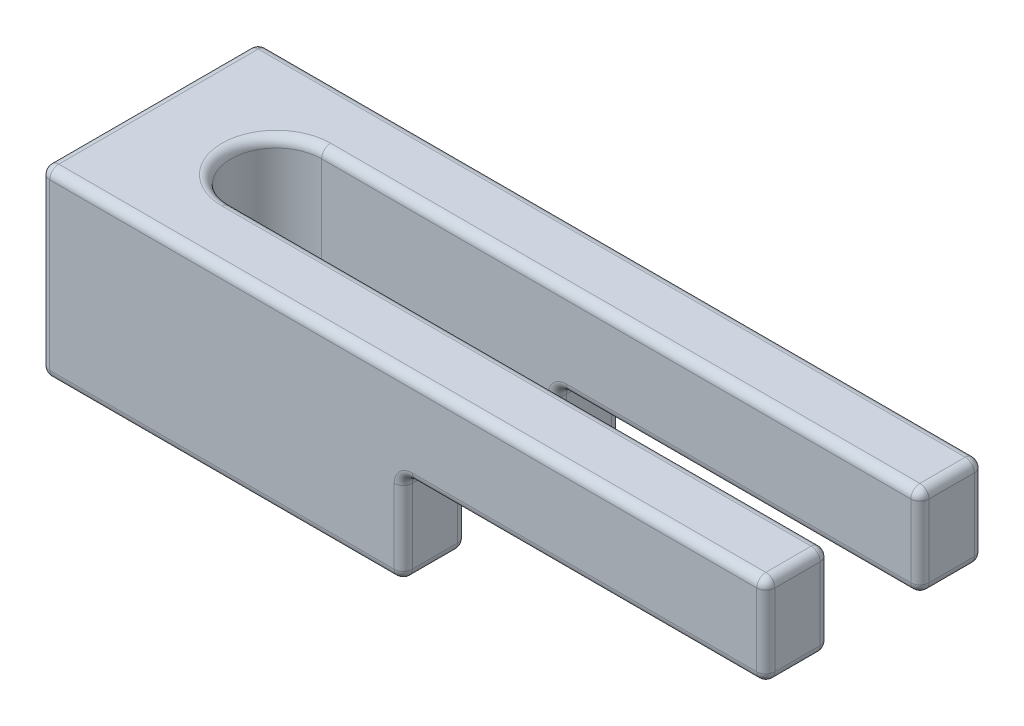
SolidWorks part; units mm, degrees
ref_plane "Plan de face" through (0, 0, 0) normal (0, 0, 1) x (1, 0, 0)
ref_plane "Plan de dessus" through (0, 0, 0) normal (0, 1, 0) x (1, 0, 0)
ref_plane "Plan de droite" through (0, 0, 0) normal (1, 0, 0) x (0, 0, -1)
sketch "Esquisse1" plane through (0, 0, 0) normal (0, 1, 0) x (1, 0, 0)
  line L0 (-88, 0) -> (88, 0) construction
  line L1 (-95, -6) -> (95, -6)
  line L2 (-95, -6) -> (-95, 6)
  line L3 (-95, 6) -> (95, 6)
  line L4 (95, -6) -> (95, 6)
  line L5 (-95, -6) -> (95, 6) construction
  line L6 (-95, 6) -> (95, -6) construction
  line L7 (-88, 2.5) -> (88, 2.5)
  line L8 (-88, -2.5) -> (88, -2.5)
  arc A0 (-88, 2.5) -> (-88, -2.5) centre (-88, 0) ccw
  arc A1 (88, -2.5) -> (88, 2.5) centre (88, 0) ccw
  point P0 (0, 0)
  point P8 (0, 0)
  dimension "D2" = 2.5
  dimension "D1" = 7
  dimension "D3" = 12
  dimension "D4" = 7
  dimension "D5" = 190
extrude "Boss.-Extru.1" add sketch "Esquisse1" along normal mid plane 5
sketch "Esquisse4" plane through (0, -2.5, 0) normal (0, -1, 0) x (1, 0, 0)
  line L0 (95, -6) -> (-95, -6) construction
  line L1 (-95, 6) -> (-75, 6)
  line L2 (-95, 6) -> (-95, -6)
  line L3 (-95, -6) -> (-75, -6)
  line L4 (-75, 6) -> (-75, 2.5)
  line L5 (-88, 0) -> (-95, 0) construction
  line L6 (-88, 2.5) -> (-75, 2.5)
  line L7 (-88, -2.5) -> (-75, -2.5)
  line L8 (-75, -2.5) -> (-75, -6)
  line L9 (-88, 2.5) -> (88, 2.5) construction
  line L10 (88, -2.5) -> (-88, -2.5) construction
  arc A0 (-88, 2.5) -> (-88, -2.5) centre (-88, 0) ccw
  arc A2 (-88, 2.5) -> (-88, -2.5) centre (-88, 0) ccw construction
  point P10 (-100, 0)
  dimension "D1" = 20
extrude "Boss.-Extru.3" add sketch "Esquisse4" along normal blind 5.1
mirror "Symétrie2" about plane through (0, 0, 0) normal (1, 0, 0) of "Boss.-Extru.3"
sketch "Esquisse5" plane through (-95, 0, 0) normal (-1, 0, 0) x (0, 0, 1)
  line L4 (-6, 2.5) -> (-6, -7.6)
  line L5 (-6, -7.6) -> (6, -7.6)
  line L6 (6, -7.6) -> (6, 2.5)
  line L7 (6, 2.5) -> (-6, 2.5)
  line L8 (-6, 2.5) -> (-6, -7.6)
  line L9 (-6, -7.6) -> (6, -7.6)
  line L10 (6, -7.6) -> (6, 2.5)
  line L11 (6, 2.5) -> (-6, 2.5)
  dimension "D1" = 0
extrude "Enlèv. mat.-Extru.1" cut sketch "Esquisse5" against normal through all from offset 40 offset against normal yes
fillet "Congé1" radius 0.5 34 edges at (-75, -7.6, 4.25) (-75, -7.6, -4.25) (-75, -2.5, -4.25) (-75, -2.5, 4.25) (-81.5, -7.6, 2.5) (-75, -5.05, 2.5) (-65, -2.5, 2.5) (-85, -7.6, -6) (-75, -5.05, -6) (-65, -2.5, -6) (-95, -7.6, 0) (-95, -2.55, -6) (-75, -5.05, -2.5) (-81.5, -7.6, -2.5) (-65, -2.5, -2.5) (-90.5, -7.6, 0) (-65, -2.5, 6) (-75, -5.05, 6) (-85, -7.6, 6) (-95, -2.55, 6) (-71.5, 2.5, 2.5) (-71.5, 2.5, -2.5) (-90.5, 2.5, 0) (-75, 2.5, 6) (-95, 2.5, 0) (-75, 2.5, -6) (-55, -2.5, -4.25) (-55, -2.5, 4.25) (-55, 0, 2.5) (-55, 0, -6) (-55, 0, -2.5) (-55, 0, 6) (-55, 2.5, -4.25) (-55, 2.5, 4.25)
